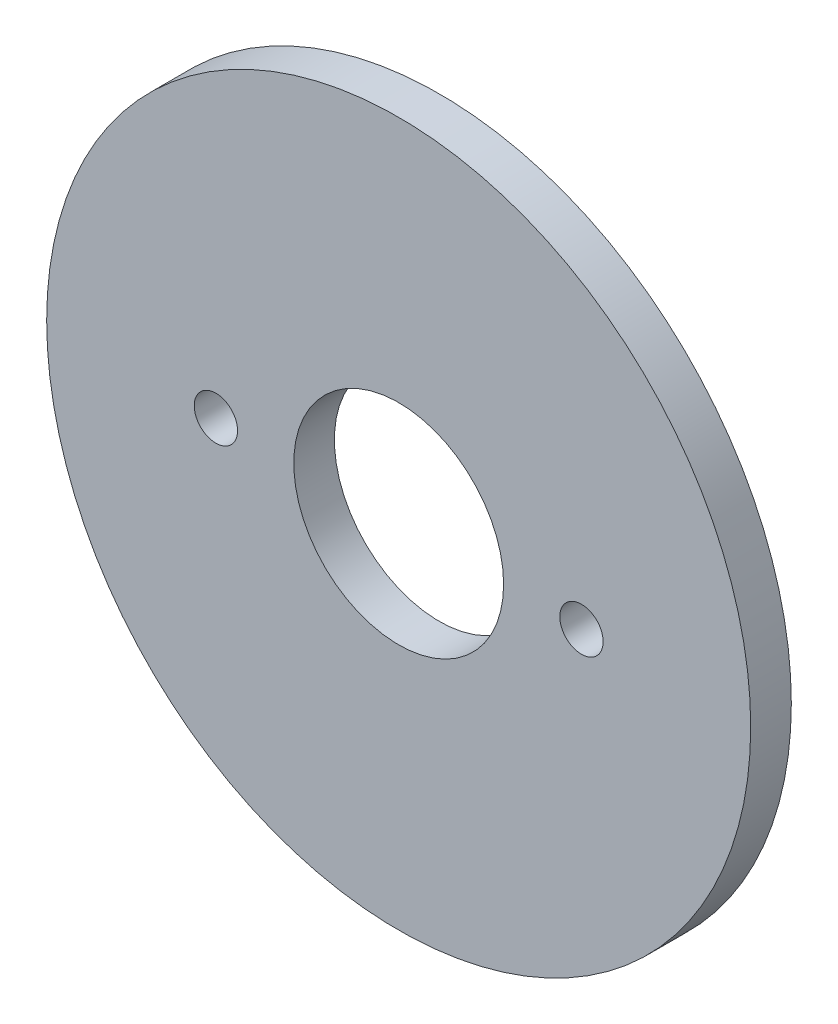
SolidWorks part; units mm, degrees
material "MDF"
ref_plane "Plano frontal" through (0, 0, 0) normal (0, 0, 1) x (1, 0, 0)
ref_plane "Plano superior" through (0, 0, 0) normal (0, 1, 0) x (1, 0, 0)
ref_plane "Plano direito" through (0, 0, 0) normal (1, 0, 0) x (0, 0, -1)
sketch "Esboço1" plane through (0, 0, 0) normal (0, 0, 1) x (1, 0, 0)
  line L0 (-13.5, 0) -> (13.5, 0) construction
  circle A0 centre (0, 0) radius 26
  circle A1 centre (0, 0) radius 7.75
  circle A2 centre (-13.5, 0) radius 1.6
  circle A3 centre (13.5, 0) radius 1.6
  dimension "D1" = 3.2
  dimension "D2" = 15.5
  dimension "D4" = 52
  dimension "D3" = 27
extrude "Ressalto-extrusão1" add sketch "Esboço1" along normal mid plane 3
